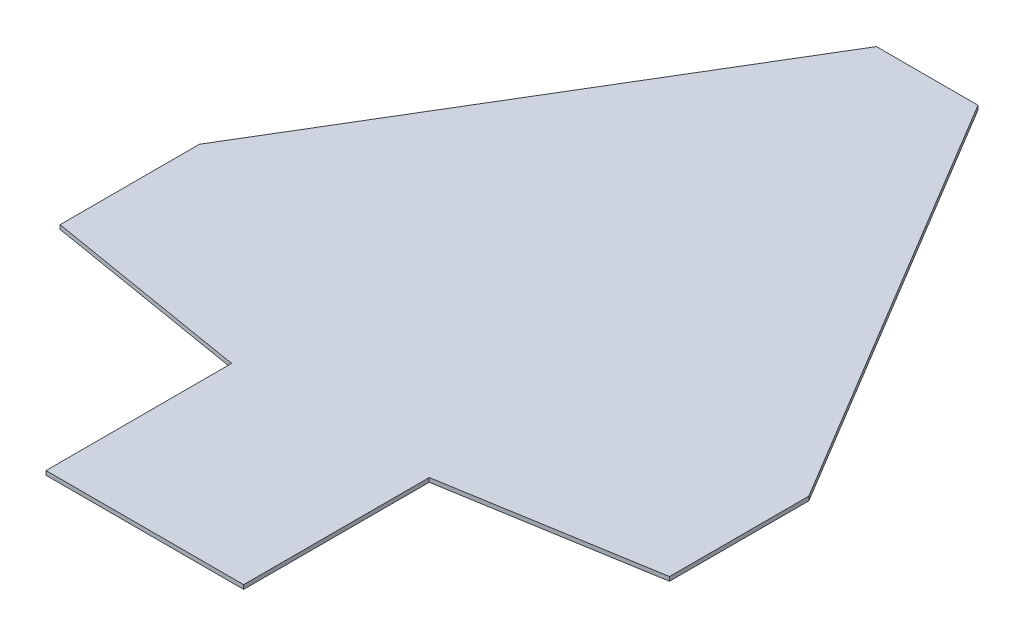
SolidWorks part; units mm, degrees
ref_plane "Front Plane" through (0, 0, 0) normal (0, 0, 1) x (1, 0, 0)
ref_plane "Top Plane" through (0, 0, 0) normal (0, 1, 0) x (1, 0, 0)
ref_plane "Right Plane" through (0, 0, 0) normal (1, 0, 0) x (0, 0, -1)
sketch "Sketch1" plane through (0, 0, 0) normal (0, 1, 0) x (1, 0, 0)
  line L6 (23.417, 82.2136) -> (23.417, -298.7864) construction
  line L18 (54.754, 82.2136) -> (-7.9201, 82.2136)
  line L24 (-37.543, -285.9104) -> (-37.543, -400.3864)
  line L27 (-37.543, -400.3864) -> (84.377, -400.3864)
  line L28 (84.377, -400.3864) -> (84.377, -285.9104)
  line L100 (211.377, -264.6967) -> (84.377, -285.9104)
  line L104 (-164.543, -264.6967) -> (-37.543, -285.9104)
  line L107 (-7.9201, 82.2136) -> (-164.543, -178.7667)
  line L108 (-164.543, -178.7667) -> (-164.543, -264.6967)
  line L114 (211.377, -178.7667) -> (211.377, -264.6967)
  line L115 (54.754, 82.2136) -> (211.377, -178.7667)
  line L120 (226.1885, 82.2136) -> (69.5655, 82.2136) construction
  line L121 (219.8385, 88.5636) -> (58.3489, 88.5636) construction
  line L122 (213.4885, 94.9136) -> (47.1323, 94.9136) construction
  line L123 (-10.0315, 78.6953) -> (-10.0315, 171.1136) construction
  line L124 (-16.3815, 80.4545) -> (-16.3815, 177.4636) construction
  line L125 (-22.7315, 82.2136) -> (-22.7315, 183.8136) construction
  line L126 (226.1885, 183.8136) -> (226.1885, 82.2136) construction
  line L127 (219.8385, 177.4636) -> (219.8385, 88.5636) construction
  line L128 (213.4885, 171.1136) -> (213.4885, 94.9136) construction
  line L129 (-10.0315, 171.1136) -> (213.4885, 171.1136) construction
  line L130 (-16.3815, 177.4636) -> (219.8385, 177.4636) construction
  line L131 (-22.7315, 183.8136) -> (226.1885, 183.8136) construction
  line L132 (58.3489, 88.5636) -> (217.727, -177.0075) construction
  line L133 (47.1323, 94.9136) -> (211.377, -178.7667) construction
  line L134 (-10.0315, 78.6953) -> (-164.543, -178.7667) construction
  line L135 (-37.543, -292.3484) -> (-37.543, -400.3864) construction
  line L136 (84.377, -400.3864) -> (84.377, -292.3484) construction
  line L137 (-164.543, -178.7667) -> (-164.543, -258.2588) construction
  line L138 (211.377, -178.7667) -> (211.377, -258.2588) construction
  line L139 (-31.193, -394.0364) -> (78.027, -394.0364) construction
  line L140 (-24.843, -387.6864) -> (71.677, -387.6864) construction
  line L141 (-31.193, -286.9711) -> (-31.193, -394.0364) construction
  line L142 (-24.843, -281.5938) -> (-24.843, -387.6864) construction
  line L143 (78.027, -394.0364) -> (78.027, -286.9711) construction
  line L144 (71.677, -387.6864) -> (71.677, -281.5938) construction
  line L145 (224.077, -269.0134) -> (84.377, -292.3484) construction
  line L146 (217.727, -263.6361) -> (78.027, -286.9711) construction
  line L147 (211.377, -258.2588) -> (71.677, -281.5938) construction
  line L148 (-170.893, -263.6361) -> (-31.193, -286.9711) construction
  line L149 (-164.543, -258.2588) -> (-24.843, -281.5938) construction
  line L150 (-177.243, -269.0134) -> (-37.543, -292.3484) construction
  line L151 (69.5655, 82.2136) -> (224.077, -175.2483) construction
  line L152 (217.727, -177.0075) -> (217.727, -263.6361) construction
  line L153 (224.077, -175.2483) -> (224.077, -269.0134) construction
  line L154 (-170.893, -177.0075) -> (-170.893, -263.6361) construction
  line L155 (-177.243, -175.2483) -> (-177.243, -269.0134) construction
  line L156 (-16.3815, 80.4545) -> (-170.893, -177.0075) construction
  line L157 (-22.7315, 82.2136) -> (-177.243, -175.2483) construction
  dimension "D2" = 6.35
  dimension "D3" = 12.7
extrude "Boss-Extrude1" add sketch "Sketch1" along normal blind 2.54
